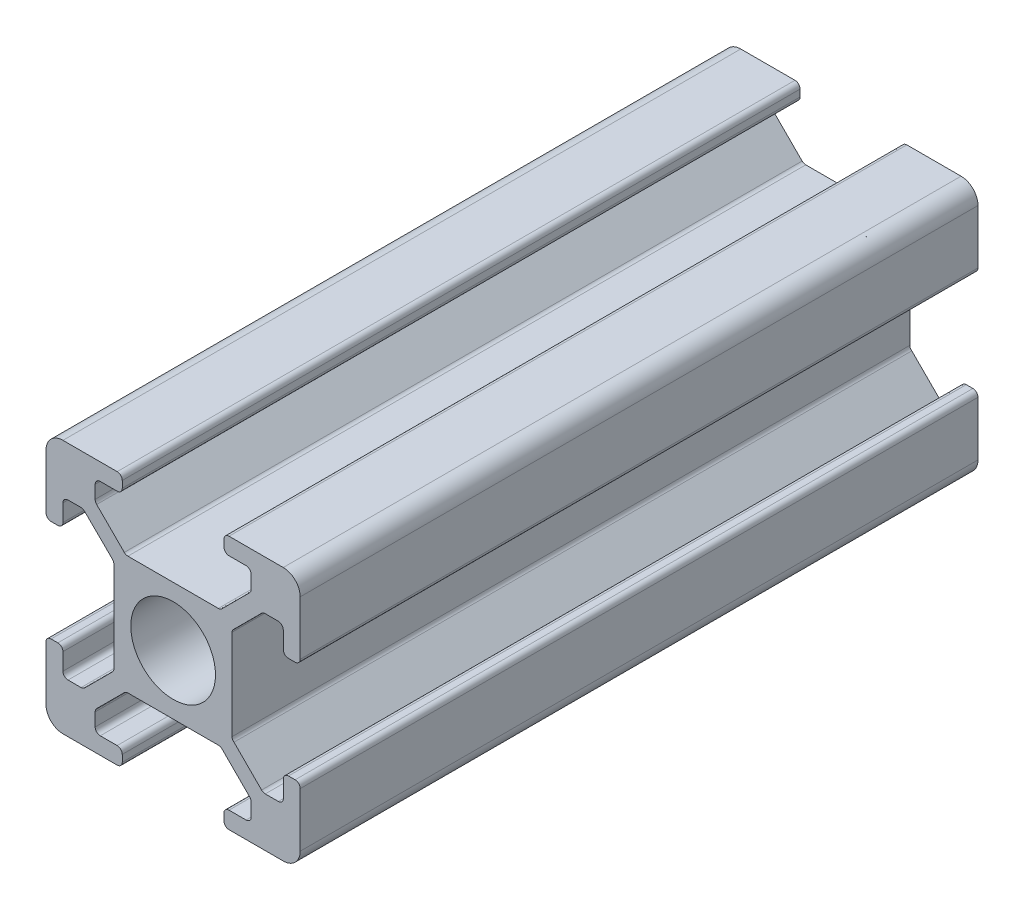
SolidWorks part; units mm, degrees
ref_plane "Front Plane" through (0, 0, 0) normal (0, 0, 1) x (1, 0, 0)
ref_plane "Top Plane" through (0, 0, 0) normal (0, 1, 0) x (1, 0, 0)
ref_plane "Right Plane" through (0, 0, 0) normal (1, 0, 0) x (0, 0, -1)
sketch "Sketch1" plane through (0, 0, 0) normal (0, 0, 1) x (1, 0, 0)
  line L0 (0.9971, -0.011) -> (4.1971, -0.011)
  line L1 (14.9971, 0.989) -> (14.9971, 4.189)
  line L2 (13.9971, 14.989) -> (10.7971, 14.989)
  line L3 (-0.0029, 13.989) -> (-0.0029, 10.789)
  line L4 (4.4971, 0.289) -> (4.4971, 0.689)
  line L5 (10.4971, 0.289) -> (10.4971, 0.689)
  line L6 (4.4971, 14.689) -> (4.4971, 14.289)
  line L7 (10.4971, 14.689) -> (10.4971, 14.289)
  line L8 (4.1971, 14.989) -> (0.9971, 14.989)
  line L9 (10.7971, -0.011) -> (13.9971, -0.011)
  line L10 (0.9971, 4.189) -> (0.9971, 3.189)
  line L11 (0.9971, 10.789) -> (0.9971, 11.7902)
  line L12 (14.6971, 10.5) -> (14.3, 10.5)
  line L13 (14.6971, 4.489) -> (14.3053, 4.489)
  line L14 (0.2971, 4.489) -> (0.6971, 4.489)
  line L15 (0.2971, 10.489) -> (0.6971, 10.489)
  line L16 (-0.0029, 4.189) -> (-0.0029, 0.989)
  line L17 (14.9971, 10.8) -> (14.9971, 13.989)
  line L18 (14, 10.8) -> (14, 11.8)
  line L19 (14.0053, 4.189) -> (14.0053, 3.189)
  line L20 (4.8302, 10.985) -> (10.1675, 10.985)
  line L21 (10.9699, 10.1634) -> (10.9699, 4.8261)
  line L22 (10.1715, 3.9947) -> (4.8343, 3.9947)
  line L23 (4.0029, 4.8261) -> (4.0029, 10.1634)
  line L24 (4.1971, 13.989) -> (3.1971, 13.989)
  line L25 (10.7971, 13.989) -> (11.7988, 13.989)
  line L26 (4.1971, 0.989) -> (3.1971, 0.989)
  line L27 (10.7971, 0.989) -> (11.8086, 0.989)
  line L28 (1.2971, 12.0902) -> (2.0579, 12.0902)
  line L29 (2.8971, 13.689) -> (2.8971, 12.9204)
  line L30 (1.2971, 2.889) -> (2.0658, 2.889)
  line L31 (2.8971, 1.289) -> (2.8971, 2.0576)
  line L32 (4.6181, 11.0728) -> (2.9867, 12.7042)
  line L33 (3.9121, 10.3808) -> (2.2729, 12.0018)
  line L34 (10.3796, 11.0728) -> (12.011, 12.7042)
  line L35 (11.0879, 10.3808) -> (12.7192, 12.0121)
  line L36 (11.0891, 4.6099) -> (12.7204, 2.9786)
  line L37 (10.3877, 3.9052) -> (12.0191, 2.2738)
  line L38 (4.6181, 3.9052) -> (2.9867, 2.2738)
  line L39 (3.9133, 4.6099) -> (2.282, 2.9786)
  line L40 (12.0988, 13.689) -> (12.0988, 12.9163)
  line L41 (13.7, 12.1) -> (12.9314, 12.1)
  line L42 (13.7053, 2.889) -> (12.9366, 2.889)
  line L43 (12.1086, 1.289) -> (12.1086, 2.0576)
  circle A0 centre (7.5, 7.5) radius 2.5
  arc A1 (0.9971, -0.011) -> (-0.0029, 0.989) centre (0.9971, 0.989) cw
  arc A2 (13.9971, -0.011) -> (14.9971, 0.989) centre (13.9971, 0.989) ccw
  arc A3 (14.9971, 13.989) -> (13.9971, 14.989) centre (13.9971, 13.989) ccw
  arc A4 (0.9971, 14.989) -> (-0.0029, 13.989) centre (0.9971, 13.989) ccw
  arc A5 (10.4971, 0.289) -> (10.7971, -0.011) centre (10.7971, 0.289) ccw
  arc A6 (10.4971, 0.689) -> (10.7971, 0.989) centre (10.7971, 0.689) cw
  arc A7 (4.4971, 0.289) -> (4.1971, -0.011) centre (4.1971, 0.289) cw
  arc A8 (4.4971, 0.689) -> (4.1971, 0.989) centre (4.1971, 0.689) ccw
  arc A9 (0.6971, 4.489) -> (0.9971, 4.189) centre (0.6971, 4.189) cw
  arc A10 (0.2971, 4.489) -> (-0.0029, 4.189) centre (0.2971, 4.189) ccw
  arc A11 (0.6971, 10.489) -> (0.9971, 10.789) centre (0.6971, 10.789) ccw
  arc A12 (0.2971, 10.489) -> (-0.0029, 10.789) centre (0.2971, 10.789) cw
  arc A13 (4.4971, 14.289) -> (4.1971, 13.989) centre (4.1971, 14.289) cw
  arc A14 (4.1971, 14.989) -> (4.4971, 14.689) centre (4.1971, 14.689) cw
  arc A15 (10.4971, 14.289) -> (10.7971, 13.989) centre (10.7971, 14.289) ccw
  arc A16 (10.7971, 14.989) -> (10.4971, 14.689) centre (10.7971, 14.689) ccw
  arc A17 (14.3053, 4.489) -> (14.0053, 4.189) centre (14.3053, 4.189) ccw
  arc A18 (14.9971, 4.189) -> (14.6971, 4.489) centre (14.6971, 4.189) ccw
  arc A19 (14.3, 10.5) -> (14, 10.8) centre (14.3, 10.8) cw
  arc A20 (14.9971, 10.8) -> (14.6971, 10.5) centre (14.6971, 10.8) cw
  arc A21 (11.7988, 13.989) -> (12.0988, 13.689) centre (11.7988, 13.689) cw
  arc A22 (14, 11.8) -> (13.7, 12.1) centre (13.7, 11.8) ccw
  arc A23 (14.0053, 3.189) -> (13.7053, 2.889) centre (13.7053, 3.189) cw
  arc A24 (11.8086, 0.989) -> (12.1086, 1.289) centre (11.8086, 1.289) ccw
  arc A25 (3.1971, 0.989) -> (2.8971, 1.289) centre (3.1971, 1.289) cw
  arc A26 (0.9971, 3.189) -> (1.2971, 2.889) centre (1.2971, 3.189) ccw
  arc A27 (0.9971, 11.7902) -> (1.2971, 12.0902) centre (1.2971, 11.7902) cw
  arc A28 (3.1971, 13.989) -> (2.8971, 13.689) centre (3.1971, 13.689) ccw
  arc A29 (10.3796, 11.0728) -> (10.1675, 10.985) centre (10.1675, 11.285) cw
  arc A30 (12.0988, 12.9163) -> (12.011, 12.7042) centre (11.7988, 12.9163) cw
  arc A31 (4.6181, 11.0728) -> (4.8302, 10.985) centre (4.8302, 11.285) ccw
  arc A32 (12.9314, 12.1) -> (12.7192, 12.0121) centre (12.9314, 11.8) ccw
  arc A33 (10.9699, 10.1634) -> (11.0879, 10.3808) centre (11.2692, 10.1417) cw
  arc A34 (11.0891, 4.6099) -> (10.9699, 4.8261) centre (11.269, 4.85) cw
  arc A35 (12.9366, 2.889) -> (12.7204, 2.9786) centre (12.9366, 3.1947) cw
  arc A36 (12.1086, 2.0576) -> (12.0191, 2.2738) centre (11.8029, 2.0576) ccw
  arc A37 (2.8971, 2.0576) -> (2.9867, 2.2738) centre (3.2029, 2.0576) cw
  arc A38 (10.3877, 3.9052) -> (10.1715, 3.9947) centre (10.1715, 3.689) ccw
  arc A39 (4.6181, 3.9052) -> (4.8343, 3.9947) centre (4.8343, 3.689) cw
  arc A40 (2.0658, 2.889) -> (2.282, 2.9786) centre (2.0658, 3.1947) ccw
  arc A41 (3.9133, 4.6099) -> (4.0029, 4.8261) centre (3.6971, 4.8261) ccw
  arc A42 (3.9121, 10.3808) -> (4.0029, 10.1634) centre (3.6971, 10.1634) cw
  arc A43 (2.8971, 12.9204) -> (2.9867, 12.7042) centre (3.2029, 12.9204) ccw
  arc A44 (2.0579, 12.0902) -> (2.2729, 12.0018) centre (2.0579, 11.7845) cw
extrude "Boss-Extrude1" add sketch "Sketch1" along normal blind 40
